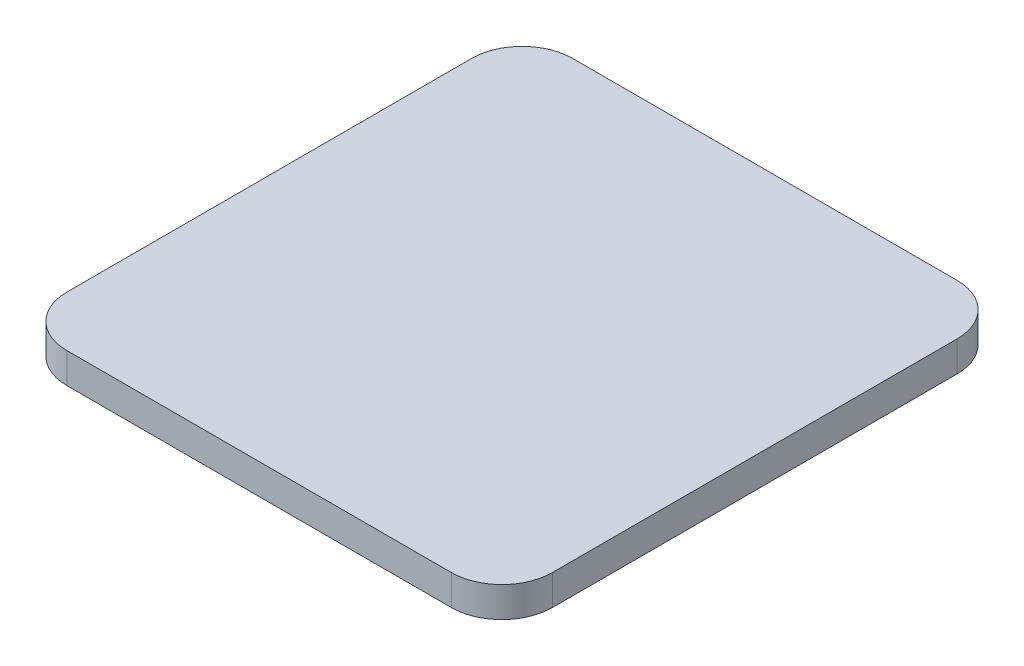
SolidWorks part; units mm, degrees
ref_plane "Front Plane" through (0, 0, 0) normal (0, 0, 1) x (1, 0, 0)
ref_plane "Top Plane" through (0, 0, 0) normal (0, 1, 0) x (1, 0, 0)
ref_plane "Right Plane" through (0, 0, 0) normal (1, 0, 0) x (0, 0, -1)
sketch "Sketch1" plane through (0, 21.8233, 0) normal (0, -1, 0) x (1, 0, 0)
  line L8 (13.9215, 28.2805) -> (51.9215, 28.2805)
  line L9 (56.9215, 33.2805) -> (56.9215, 73.2805)
  line L10 (51.9215, 78.2805) -> (13.9215, 78.2805)
  line L11 (8.9215, 73.2805) -> (8.9215, 33.2805)
  line L12 (13.9215, 28.2805) -> (51.9215, 28.2805)
  line L13 (56.9215, 33.2805) -> (56.9215, 73.2805)
  line L14 (51.9215, 78.2805) -> (13.9215, 78.2805)
  line L15 (8.9215, 73.2805) -> (8.9215, 33.2805)
  arc A8 (8.9215, 33.2805) -> (13.9215, 28.2805) centre (13.9215, 33.2805) ccw
  arc A9 (51.9215, 28.2805) -> (56.9215, 33.2805) centre (51.9215, 33.2805) ccw
  arc A10 (56.9215, 73.2805) -> (51.9215, 78.2805) centre (51.9215, 73.2805) ccw
  arc A11 (13.9215, 78.2805) -> (8.9215, 73.2805) centre (13.9215, 73.2805) ccw
  arc A12 (8.9215, 33.2805) -> (13.9215, 28.2805) centre (13.9215, 33.2805) ccw
  arc A13 (51.9215, 28.2805) -> (56.9215, 33.2805) centre (51.9215, 33.2805) ccw
  arc A14 (56.9215, 73.2805) -> (51.9215, 78.2805) centre (51.9215, 73.2805) ccw
  arc A15 (13.9215, 78.2805) -> (8.9215, 73.2805) centre (13.9215, 73.2805) ccw
  dimension "D1" = 0
extrude "Boss-Extrude1" add sketch "Sketch1" along normal blind 3
other "Cavity1"
other "Hirose-RPC1<1>@SolderingController1"
